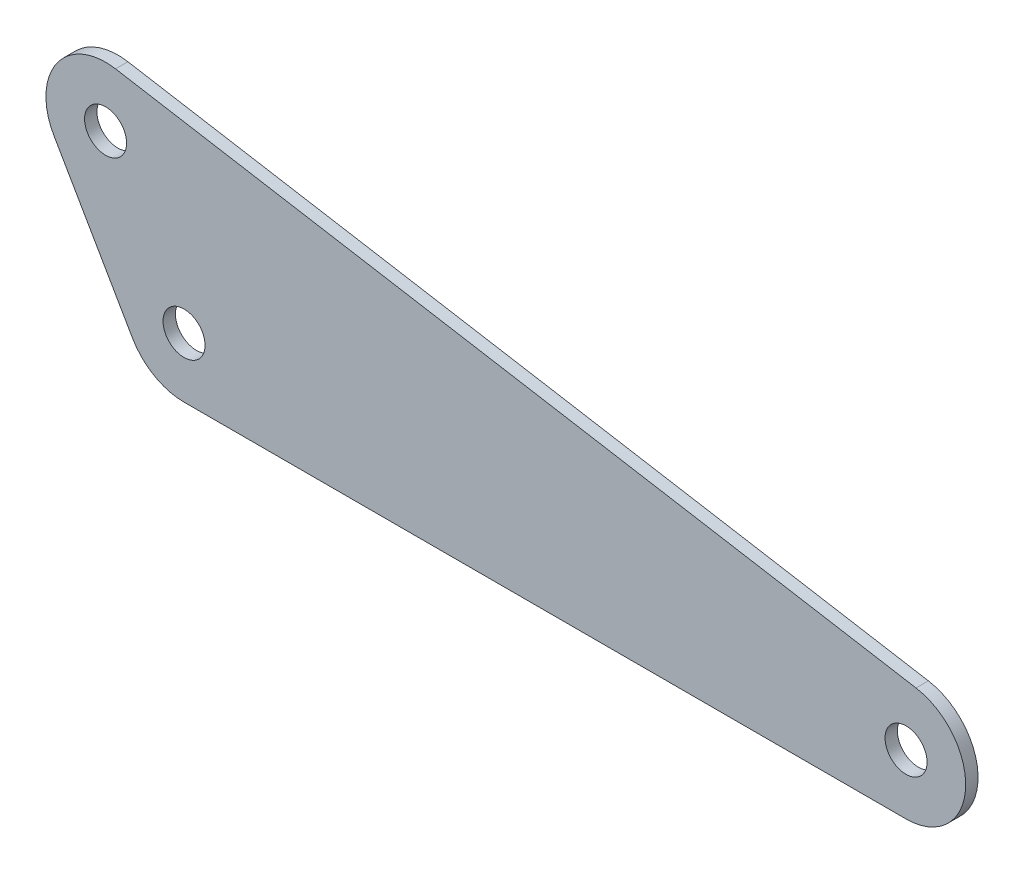
SolidWorks part; units mm, degrees
material "Acrylic (Medium-high impact)"
ref_plane "Front Plane" through (0, 0, 0) normal (0, 0, 1) x (1, 0, 0)
ref_plane "Top Plane" through (0, 0, 0) normal (0, 1, 0) x (1, 0, 0)
ref_plane "Right Plane" through (0, 0, 0) normal (1, 0, 0) x (0, 0, -1)
sketch "Sketch1" plane through (0, 0, 0) normal (0, 0, 1) x (1, 0, 0)
  line L0 (0, 0) -> (-31.75, 54.9926) construction
  line L1 (-31.75, 54.9926) -> (292.1, 0) construction
  line L2 (292.1, 0) -> (0, 0) construction
  line L3 (0, -31.75) -> (292.1, -31.75)
  line L4 (-26.4347, 86.2945) -> (297.4153, 31.3019)
  line L5 (-59.2463, 39.1176) -> (-27.4963, -15.875)
  arc A0 (-27.4963, -15.875) -> (0, -31.75) centre (0, 0) ccw
  arc A1 (292.1, -31.75) -> (297.4153, 31.3019) centre (292.1, 0) ccw
  arc A2 (-26.4347, 86.2945) -> (-59.2463, 39.1176) centre (-31.75, 54.9926) ccw
  circle A3 centre (-31.75, 54.9926) radius 8.5
  circle A4 centre (0, 0) radius 8.5
  circle A5 centre (292.1, 0) radius 8.5
  dimension "D1" = 63.5
  dimension "D2" = 60
  dimension "D4" = 17
  dimension "D3" = 292.1
extrude "Boss-Extrude1" add sketch "Sketch1" along normal blind 5
sketch "Sketch2" plane through (0, 0, 5) normal (0, 0, 1) x (1, 0, 0)
  line L0 (297.4153, 31.3019) -> (-26.4347, 86.2945) construction
  line L1 (-59.2463, 39.1176) -> (-27.4963, -15.875) construction
  line L2 (0, -31.75) -> (292.1, -31.75) construction
  line L3 (297.4153, 31.3019) -> (-26.4347, 86.2945)
  line L4 (-59.2463, 39.1176) -> (-27.4963, -15.875)
  line L5 (0, -31.75) -> (292.1, -31.75)
  line L6 (296.1397, 23.7895) -> (-27.7103, 78.7821)
  line L7 (-52.6472, 42.9276) -> (-20.8972, -12.065)
  line L8 (0, -24.13) -> (292.1, -24.13)
  arc A0 (-26.4347, 86.2945) -> (-59.2463, 39.1176) centre (-31.75, 54.9926) ccw construction
  arc A1 (-27.4963, -15.875) -> (0, -31.75) centre (0, 0) ccw construction
  arc A2 (292.1, -31.75) -> (297.4153, 31.3019) centre (292.1, 0) ccw construction
  arc A3 (-26.4347, 86.2945) -> (-59.2463, 39.1176) centre (-31.75, 54.9926) ccw
  arc A4 (-27.4963, -15.875) -> (0, -31.75) centre (0, 0) ccw
  arc A5 (292.1, -31.75) -> (297.4153, 31.3019) centre (292.1, 0) ccw
  arc A6 (-27.7103, 78.7821) -> (-52.6472, 42.9276) centre (-31.75, 54.9926) ccw
  arc A7 (-20.8972, -12.065) -> (0, -24.13) centre (0, 0) ccw
  arc A8 (292.1, -24.13) -> (296.1397, 23.7895) centre (292.1, 0) ccw
  dimension "D1" = 7.62
extrude "Cut-Extrude1" cut sketch "Sketch2" against normal through all
